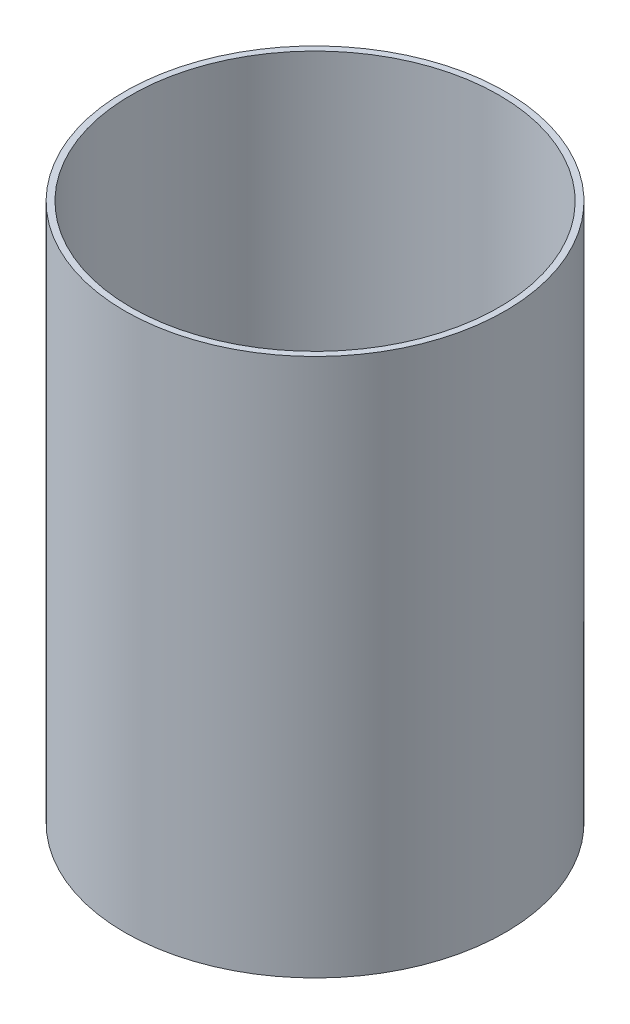
SolidWorks part; units mm, degrees
material "PET"
ref_plane "Front Plane" through (0, 0, 0) normal (0, 0, 1) x (1, 0, 0)
ref_plane "Top Plane" through (0, 0, 0) normal (0, 1, 0) x (1, 0, 0)
ref_plane "Right Plane" through (0, 0, 0) normal (1, 0, 0) x (0, 0, -1)
sketch "Sketch1" plane through (0, 0, 0) normal (0, 1, 0) x (1, 0, 0)
  circle A0 centre (0, 0) radius 92.71
  circle A1 centre (0, 0) radius 53.975
  dimension "D1" = 185.42
  dimension "D2" = 107.95
extrude "Top of Hatch" add sketch "Sketch1" along normal blind 3.302
sketch "Sketch2" plane through (0, 3.302, 0) normal (0, 1, 0) x (1, 0, 0)
  circle A0 centre (0, 0) radius 92.71
  circle A1 centre (0, 0) radius 89.662
  circle A2 centre (0, 0) radius 92.71 construction
  dimension "D1" = 3.048
extrude "Hatch Body" add sketch "Sketch2" along normal blind 259.08
sketch "Sketch3" plane through (0, 0, 0) normal (0, -1, 0) x (1, 0, 0)
  line L0 (0, 0) -> (-75.565, 0) construction
  line L1 (0, 0) -> (0, 76.902) construction
  circle A0 centre (-75.565, 0) radius 13.97
  circle A1 centre (75.565, 0) radius 13.97
  dimension "D1" = 75.565
  dimension "D2" = 27.94
extrude "Charge Tube Holes" cut sketch "Sketch3" against normal up to surface (3.302 mm away) up to face at (0, 3.302, 53.975)
sketch "Sketch4" plane through (0, 0, 0) normal (0, -1, 0) x (1, 0, 0)
  circle A0 centre (38.1, 65.9911) radius 3.81
  circle A1 centre (-38.1, 65.9911) radius 3.81
  circle A2 centre (-38.1, -65.9911) radius 3.81
  circle A3 centre (38.1, -65.9911) radius 3.81
  dimension "D1" = 76.2
  dimension "D3" = 7.62
  dimension "D4" = 76.2
  dimension "D6" = 7.62
  dimension "D9" = 7.62
  dimension "D12" = 7.62
  dimension "D2" = 38.1
  dimension "D5" = 38.1
  dimension "D7" = 76.2
  dimension "D8" = 38.1
  dimension "D10" = 76.2
  dimension "D11" = 38.1
extrude "Bolt Holes" cut sketch "Sketch4" against normal through all
sketch "Sketch 5" plane through (0, 0, 0) normal (0, -1, 0) x (1, 0, 0)
  circle A0 centre (-26.1124, 57.3248) radius 5.08
  circle A1 centre (9.1936, 61.0335) radius 5.08
  dimension "D1" = 10.16
  dimension "D2" = 10.16
  dimension "D3" = 62.992
  dimension "D4" = 61.722
  dimension "D5" = 26.1124
  dimension "D6" = 35.306
extrude "Antenna Holes " cut sketch "Sketch 5" against normal through all
